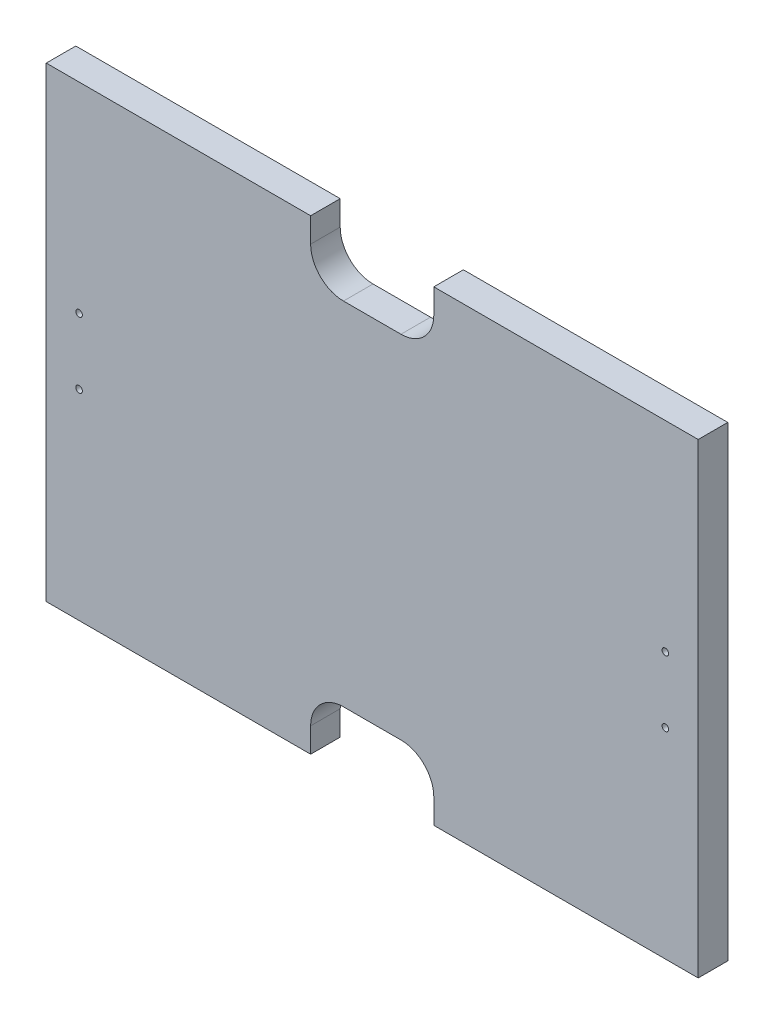
SolidWorks part; units mm, degrees
ref_plane "Front Plane" through (0, 0, 0) normal (0, 0, 1) x (1, 0, 0)
ref_plane "Top Plane" through (0, 0, 0) normal (0, 1, 0) x (1, 0, 0)
ref_plane "Right Plane" through (0, 0, 0) normal (1, 0, 0) x (0, 0, -1)
sketch "Sketch1" plane through (0, 0, 0) normal (0, 0, 1) x (1, 0, 0)
  line L1 (0, 0) -> (397, 0)
  line L2 (0, 0) -> (0, 284)
  line L3 (0, 284) -> (397, 284)
  line L4 (397, 0) -> (397, 284)
  dimension "D1" = 284
  dimension "D2" = 397
extrude "Boss-Extrude1" add sketch "Sketch1" along normal blind 18
sketch "Sketch2" plane through (0, 0, 18) normal (0, 0, 1) x (1, 0, 0)
  line L0 (397, 284) -> (0, 284) construction
  line L1 (236, 284) -> (161, 284)
  line L2 (236, 284) -> (236, 269)
  line L3 (216, 249) -> (181, 249)
  line L4 (161, 284) -> (161, 269)
  line L5 (0, 284) -> (0, 0) construction
  line L6 (198.5, 284) -> (198.5, 0) construction
  line L7 (0, 0) -> (397, 0) construction
  line L8 (0, 142) -> (397, 142) construction
  line L9 (397, 0) -> (397, 284) construction
  line L10 (216, 35) -> (181, 35)
  line L11 (161, 0) -> (161, 15)
  line L12 (236, 0) -> (161, 0)
  line L13 (236, 0) -> (236, 15)
  circle A0 centre (20, 162) radius 2
  circle A1 centre (20, 122) radius 2
  circle A2 centre (377, 122) radius 2
  circle A3 centre (377, 162) radius 2
  arc A4 (216, 35) -> (236, 15) centre (216, 15) cw
  arc A5 (181, 35) -> (161, 15) centre (181, 15) ccw
  arc A6 (236, 269) -> (216, 249) centre (216, 269) cw
  arc A7 (181, 249) -> (161, 269) centre (181, 269) cw
  point P6 (198.5, 284)
  point P7 (198.5, 249)
  point P14 (0, 142)
  point P33 (236, 35)
  point P36 (161, 35)
  point P39 (236, 249)
  point P42 (161, 249)
  dimension "D6" = 4
  dimension "D7" = 20
  dimension "D1" = 35
  dimension "D2" = 75
  dimension "D3" = 20
  dimension "D4" = 40
  dimension "D5" = 20
extrude "Cut-Extrude1" cut sketch "Sketch2" against normal through all
